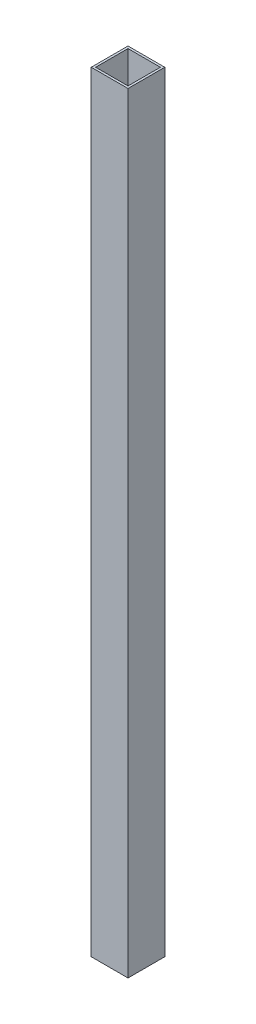
SolidWorks part; units mm, degrees
ref_plane "Front Plane" through (0, 0, 0) normal (0, 0, 1) x (1, 0, 0)
ref_plane "Top Plane" through (0, 0, 0) normal (0, 1, 0) x (1, 0, 0)
ref_plane "Right Plane" through (0, 0, 0) normal (1, 0, 0) x (0, 0, -1)
sketch "Sketch1" plane through (0, 0, 0) normal (0, 1, 0) x (1, 0, 0)
  line L0 (3, 3) -> (47, 3)
  line L1 (0, 0) -> (50, 0)
  line L2 (0, 0) -> (0, 50)
  line L3 (0, 50) -> (50, 50)
  line L4 (50, 0) -> (50, 50)
  line L5 (47, 3) -> (47, 47)
  line L6 (3, 47) -> (47, 47)
  line L7 (3, 3) -> (3, 47)
  dimension "D1" = 50
  dimension "D2" = 3
extrude "Boss-Extrude1" add sketch "Sketch1" along normal blind 1047
